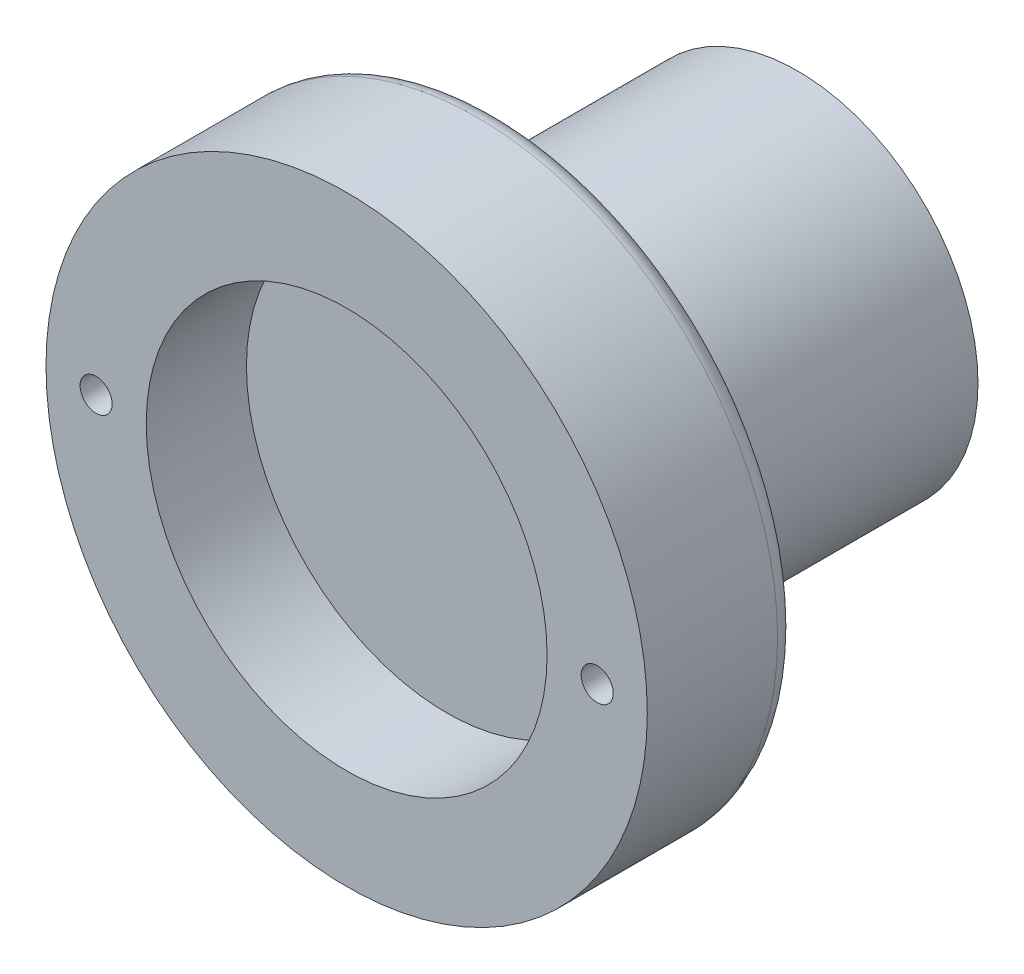
SolidWorks part; units mm, degrees
ref_plane "Front Plane" through (0, 0, 0) normal (0, 0, 1) x (1, 0, 0)
ref_plane "Top Plane" through (0, 0, 0) normal (0, 1, 0) x (1, 0, 0)
ref_plane "Right Plane" through (0, 0, 0) normal (1, 0, 0) x (0, 0, -1)
sketch "Sketch1" plane through (0, 0, 0) normal (0, 0, 1) x (1, 0, 0)
  line L0 (-25, 0) -> (0, 0) construction
  line L1 (0, 0) -> (25, 0) construction
  circle A0 centre (0, 0) radius 30
  circle A1 centre (-25, 0) radius 1.6
  circle A2 centre (25, 0) radius 1.6
  dimension "D1" = 25
extrude "Boss-Extrude1" add sketch "Sketch1" along normal blind 15
sketch "Sketch2" plane through (0, 0, 15) normal (0, 0, 1) x (1, 0, 0)
  circle A0 centre (0, 0) radius 20
extrude "Cut-Extrude1" cut sketch "Sketch2" against normal blind 10
sketch "Sketch3" plane through (0, 0, 0) normal (0, 0, -1) x (-1, 0, 0)
  circle A0 centre (0, 0) radius 18
extrude "Boss-Extrude2" add sketch "Sketch3" along normal blind 30
sketch "Sketch4" plane through (0, 0, -30) normal (0, 0, -1) x (-1, 0, 0)
  circle A0 centre (0, 0) radius 16
extrude "Cut-Extrude2" cut sketch "Sketch4" against normal blind 25
fillet "Fillet2" radius 2 1 edges at (30, 0, 0)
